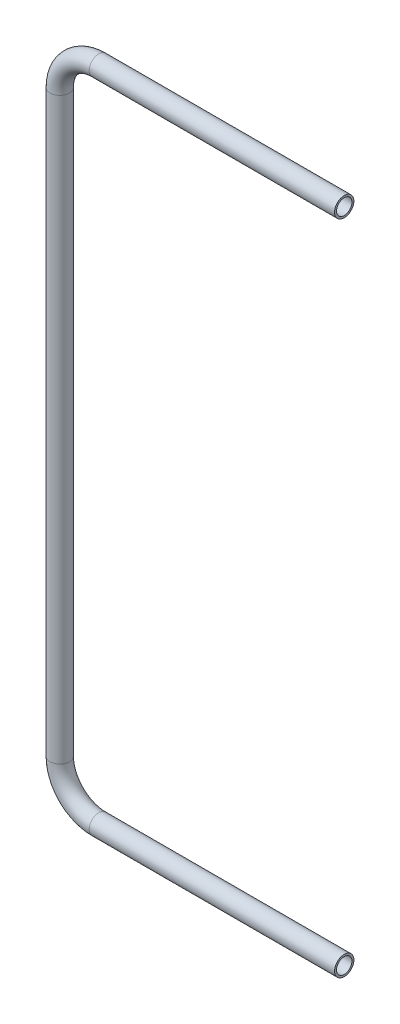
SolidWorks part; units mm, degrees
material "6061-T6 (SS)"
ref_plane "Front Plane" through (0, 0, 0) normal (0, 0, 1) x (1, 0, 0)
ref_plane "Top Plane" through (0, 0, 0) normal (0, 1, 0) x (1, 0, 0)
ref_plane "Right Plane" through (0, 0, 0) normal (1, 0, 0) x (0, 0, -1)
sketch "Sketch1" plane through (0, 0, 0) normal (0, 0, 1) x (1, 0, 0)
  line L0 (0, 0) -> (-423.799, 0)
  line L1 (-491.2995, 67.5005) -> (-491.2995, 1067.562)
  line L2 (-423.799, 1135.0625) -> (0, 1135.0625)
  arc A0 (-423.799, 0) -> (-491.2995, 67.5005) centre (-423.799, 67.5005) cw
  arc A1 (-423.799, 1135.0625) -> (-491.2995, 1067.562) centre (-423.799, 1067.562) ccw
  dimension "D1" = 67.5005
  dimension "D2" = 67.5005
  dimension "D3" = 491.2995
  dimension "D4" = 1135.0625
sketch "Sketch2" plane through (0, 0, 0) normal (1, 0, 0) x (0, 0, -1)
  circle A0 centre (0, 0) radius 16.7005
  circle A1 centre (0, 0) radius 13.335
  dimension "D1" = 33.401
  dimension "D2" = 26.67
sweep "Sweep1" add profiles "Sketch2" path "Sketch1"
